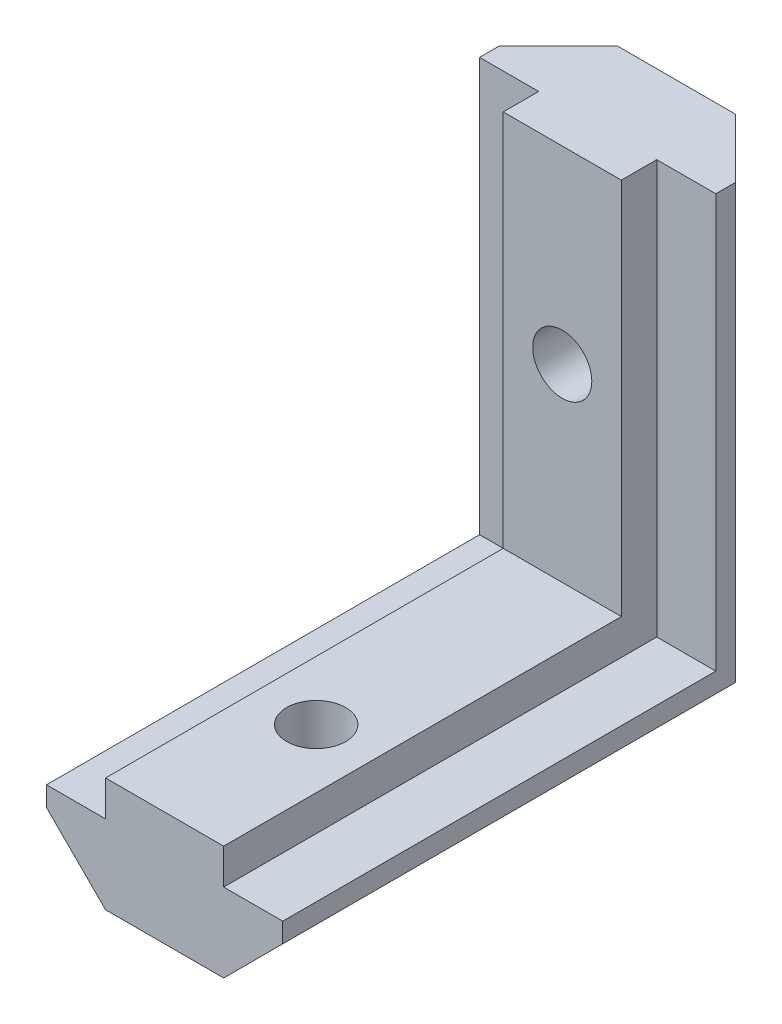
SolidWorks part; units mm, degrees
material "Lega 6061"
ref_plane "Piano frontale" through (0, 0, 0) normal (0, 0, 1) x (1, 0, 0)
ref_plane "Piano superiore" through (0, 0, 0) normal (0, 1, 0) x (1, 0, 0)
ref_plane "Piano destro" through (0, 0, 0) normal (1, 0, 0) x (0, 0, -1)
sketch "Schizzo1" plane through (0, 0, 0) normal (0, 0, 1) x (1, 0, 0)
  line L0 (3, 0) -> (-3, 0)
  line L1 (-3, 0) -> (-6, 3)
  line L2 (-6, 3) -> (-6, 4)
  line L3 (-6, 4) -> (-3, 4)
  line L4 (-3, 4) -> (-3, 5.8)
  line L5 (-3, 5.8) -> (3, 5.8)
  line L7 (0, -55) -> (0, 55) construction
  line L8 (3, 4) -> (3, 5.8)
  line L9 (6, 4) -> (3, 4)
  line L10 (6, 3) -> (6, 4)
  line L11 (3, 0) -> (6, 3)
  point P0 (0, 0)
  dimension "D1" = 5.8
  dimension "D2" = 6
  dimension "D3" = 4
  dimension "D4" = 1
  dimension "D5" = 45
  dimension "D6" = 12
extrude "Estrusione-Estrusione1" add sketch "Schizzo1" along normal blind 26
sketch "Schizzo2" plane through (0, 0, 0) normal (0, 1, 0) x (1, 0, 0)
  line L1 (3, 0) -> (6, -3)
  line L2 (6, -3) -> (6, -4)
  line L3 (6, -4) -> (3, -4)
  line L4 (3, -4) -> (3, -5.8)
  line L11 (3, 0) -> (-3, 0)
  line L12 (3, 0) -> (-3, 0) construction
  line L13 (6, 0) -> (3, 0) construction
  line L14 (3, -5.8) -> (-3, -5.8)
  line L15 (0, -5.8) -> (0, 0) construction
  line L16 (-3, -4) -> (-3, -5.8)
  line L17 (-6, -4) -> (-3, -4)
  line L18 (-6, -3) -> (-6, -4)
  line L19 (-3, 0) -> (-6, -3)
  dimension "D1" = 4
  dimension "D2" = 5.8
  dimension "D3" = 1
  dimension "D4" = 6
  dimension "D5" = 3
  dimension "D6" = 45
extrude "Estrusione-Estrusione2" add sketch "Schizzo2" along normal blind 25
sketch "Schizzo3" plane through (0, 0, 0) normal (0, 1, 0) x (1, 0, 0)
  line L0 (-3, 0) -> (-6, -3)
  line L1 (-6, -3) -> (-6, 0)
  line L2 (-6, 0) -> (-3, 0)
  line L3 (6, -3) -> (6, 0)
  line L4 (6, 0) -> (3, 0)
  line L5 (3, 0) -> (6, -3)
extrude "Taglio-Estrusione1" cut sketch "Schizzo3" along normal blind 5
sketch "Schizzo4" plane through (0, 0, 4) normal (0, 0, 1) x (1, 0, 0)
  line L0 (-6, 3) -> (-3, 0)
  line L1 (-3, 0) -> (-6, 0)
  line L2 (-6, 0) -> (-6, 3)
  line L3 (3, 0) -> (6, 0)
  line L4 (6, 0) -> (6, 3)
  line L5 (3, 0) -> (6, 3) construction
  line L6 (6, 3) -> (3, 0) construction
  line L7 (6, 3) -> (3, 0)
extrude "Taglio-Estrusione2" cut sketch "Schizzo4" against normal blind 5
sketch "Schizzo5" plane through (0, 0, 5.8) normal (0, 0, 1) x (1, 0, 0)
  line L0 (6, 25) -> (6, 4) construction
  line L1 (-3, 25) -> (3, 25) construction
  circle A0 centre (0, 15.4) radius 1.5
  dimension "D1" = 3
  dimension "D2" = 6
  dimension "D3" = 9.6
extrude "Taglio-Estrusione3" cut sketch "Schizzo5" against normal through all contours A0
cosmetic thread "Filettatura cosmetica1" parameters "D2"=4
sketch "Schizzo6" plane through (0, 5.8, 0) normal (0, 1, 0) x (1, 0, 0)
  line L0 (-3, -5.8) -> (3, -5.8) construction
  line L1 (6, -26) -> (6, -4) construction
  circle A0 centre (0, -18.3) radius 1.5
  dimension "D1" = 12.5
  dimension "D2" = 3
  dimension "D3" = 6
extrude "Taglio-Estrusione4" cut sketch "Schizzo6" against normal through all
cosmetic thread "Filettatura cosmetica2" parameters "D2"=4
